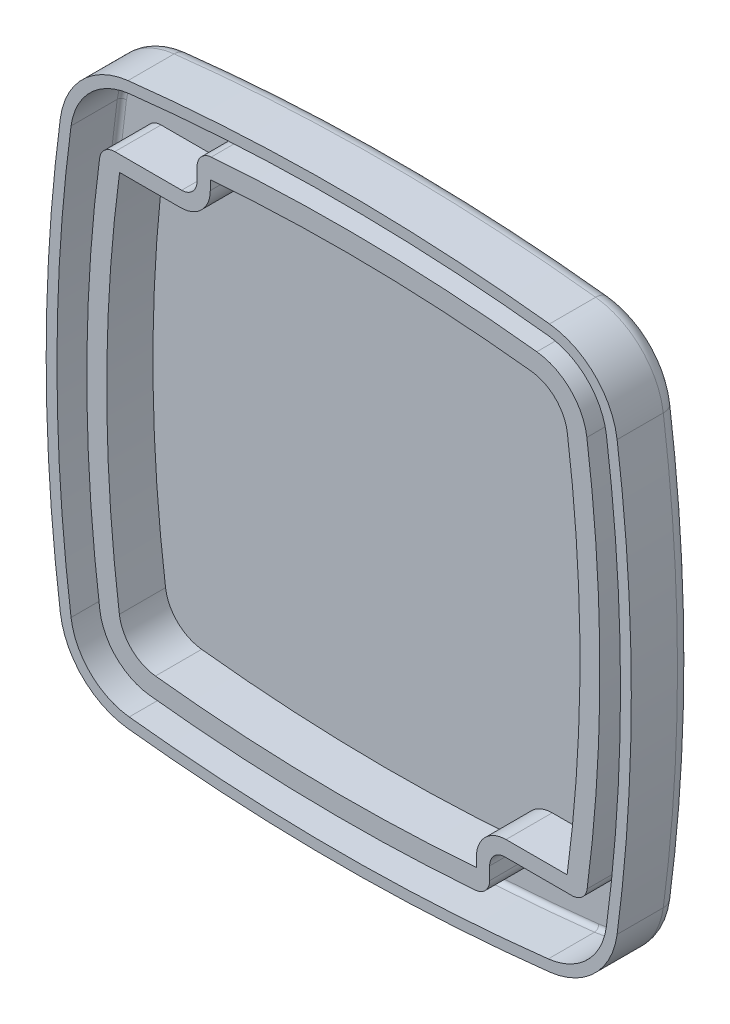
SolidWorks part; units mm, degrees
ref_plane "Ön Düzlem" through (0, 0, 0) normal (0, 0, 1) x (1, 0, 0)
ref_plane "Üst Düzlem" through (0, 0, 0) normal (0, 1, 0) x (1, 0, 0)
ref_plane "Sağ Düzlem" through (0, 0, 0) normal (1, 0, 0) x (0, 0, -1)
sketch "Çizim1" plane through (0, 0, 0) normal (0, 0, 1) x (1, 0, 0)
  line L1 (-19, -19) -> (19, -19)
  line L2 (-19, -19) -> (-19, 19)
  line L3 (-19, 19) -> (19, 19)
  line L4 (19, -19) -> (19, 19)
  line L5 (-19, -19) -> (19, 19) construction
  line L6 (-19, 19) -> (19, -19) construction
  point P0 (0, 0)
  dimension "D1" = 38
  dimension "D2" = 38
extrude "Yükseklik-Ekstrüzyon1" add sketch "Çizim1" along normal mid plane 4 contours L3 L4 L1 L2
sketch "Çizim2" plane through (0, 0, 2) normal (0, 0, 1) x (1, 0, 0)
  line L0 (-19, 17.5) -> (19, 17.5) construction
  line L1 (-19, -19) -> (-19, 19) construction
  line L2 (19, -19) -> (19, 19) construction
  line L3 (-19, 19) -> (19, 19) construction
  line L4 (0, 0) -> (12.6557, 0) construction
  line L5 (-19, 19) -> (19, 19)
  line L6 (19, 19) -> (19, 17.5)
  line L7 (-19, 19) -> (-19, 17.5)
  line L8 (-19, -17.5) -> (19, -17.5) construction
  line L9 (-19, -19) -> (-19, -17.5)
  line L10 (19, -19) -> (19, -17.5)
  line L11 (-19, -19) -> (19, -19)
  arc A0 (-19, 17.5) -> (19, 17.5) centre (0, -102.0833) cw
  arc A1 (-19, -17.5) -> (19, -17.5) centre (0, 102.0833) ccw
  line M4 (-19, 19) -> (-19, -19)
  line M5 (-19, -19) -> (19, -19)
  line M6 (19, -19) -> (19, 19)
  line M7 (19, 19) -> (-19, 19)
  dimension "D1" = 1.5
extrude "Kes-Ekstrüzyon1" cut sketch "Çizim2" against normal through all contours A0 M7 M6 | A0 L5 M4 | A1 M4 M5 | A1 L11 M6
sketch "Çizim3" plane through (0, 0, 2) normal (0, 0, 1) x (1, 0, 0)
  line L0 (17.5, 17.7287) -> (17.5, -17.7287) construction
  line L1 (19, -17.5) -> (19, 17.5) construction
  line L2 (19, 17.5) -> (19, -17.5)
  line L3 (0, 0) -> (0, -12.7146) construction
  line L4 (-17.5, 17.7287) -> (-17.5, -17.7287) construction
  line L5 (-19, 17.5) -> (-19, -17.5)
  arc A0 (19, 17.5) -> (-19, 17.5) centre (0, -102.0833) ccw construction
  arc A1 (-19, -17.5) -> (19, -17.5) centre (0, 102.0833) ccw construction
  arc A2 (17.5, 17.7287) -> (17.5, -17.7287) centre (-86.5189, 0) cw
  arc A3 (17.5, -17.7287) -> (19, -17.5) centre (0, 102.0833) ccw
  arc A4 (19, 17.5) -> (17.5, 17.7287) centre (0, -102.0833) ccw
  arc A5 (-19, 17.5) -> (-17.5, 17.7287) centre (0, -102.0833) cw
  arc A6 (-17.5, -17.7287) -> (-19, -17.5) centre (0, 102.0833) cw
  arc A7 (-17.5, 17.7287) -> (-17.5, -17.7287) centre (86.5189, 0) ccw
  arc M3 (-19, -17.5) -> (19, -17.5) centre (0, 102.0833) ccw
  line M4 (19, -17.5) -> (19, 17.5)
  arc M5 (19, 17.5) -> (-19, 17.5) centre (0, -102.0833) ccw
  line M6 (-19, 17.5) -> (-19, -17.5)
  dimension "D1" = 1.5
extrude "Kes-Ekstrüzyon2" cut sketch "Çizim3" against normal through all contours A2 L2 M5 | A2 M4 M3 | A7 L5 M3 | A7 M5 M6
fillet "Radyus1" radius 5 4 edges at (-17.5, -17.7287, 0) (17.5, -17.7287, 0) (-17.5, 17.7287, 0) (17.5, 17.7287, 0)
fillet "Radyus2" radius 1 8 edges at (16.6239, 16.8249, -2) (0, 19, -2) (-16.6239, 16.8249, -2) (-19, 0, -2) (-16.6239, -16.8249, -2) (0, -19, -2) (16.6239, -16.8249, -2) (19, 0, -2)
shell "İç Boşaltma1" thickness 0.7
sketch "Çizim10" plane through (0, 0, -1.3) normal (0, 0, 1) x (1, 0, 0)
  arc A21 (12.5637, 15.9476) -> (-12.5637, 15.9476) centre (0, -94.4838) ccw
  arc A22 (-12.5637, 15.9476) -> (-15.8151, 12.7573) centre (-12.1452, 12.2691) ccw
  arc A23 (-15.8151, 12.7573) -> (-15.8151, -12.7573) centre (80.0781, 0) ccw
  arc A24 (-15.8151, -12.7573) -> (-12.5637, -15.9476) centre (-12.1452, -12.2691) ccw
  arc A25 (-12.5637, -15.9476) -> (12.5637, -15.9476) centre (0, 94.4838) ccw
  arc A26 (12.5637, -15.9476) -> (15.8151, -12.7573) centre (12.1452, -12.2691) ccw
  arc A27 (15.8151, -12.7573) -> (15.8151, 12.7573) centre (-80.0781, 0) ccw
  arc A28 (15.8151, 12.7573) -> (12.5637, 15.9476) centre (12.1452, 12.2691) ccw
extrude "Yükseklik-Ekstrüzyon10" add sketch "Çizim10" along normal blind 3 separate body
sketch "Çizim14" plane through (0, 0, 1.7) normal (0, 0, 1) x (1, 0, 0)
  line L0 (9.5, -17.1665) -> (14.8187, -15.9691)
  line L3 (-16.5262, 13.5) -> (-9.5, 13.5)
  line L4 (-9.5, 17.1242) -> (-9.5, 13.5)
  line L5 (-9.5, 17.1242) -> (-15.4929, 15.319)
  line L6 (-15.4929, 15.319) -> (-16.5262, 13.5)
  line L7 (16.5744, -13.5) -> (9.5, -13.5)
  line L8 (9.5, -17.1665) -> (9.5, -13.5)
  line L9 (14.8187, -15.9691) -> (16.5744, -13.5)
  arc A0 (18.0784, -13.9153) -> (18.0784, 13.9153) centre (-86.5189, 0) ccw construction
  arc A1 (-13.6873, -18.2239) -> (13.6873, -18.2239) centre (0, 102.0833) ccw construction
  arc A2 (13.6873, 18.2239) -> (-13.6873, 18.2239) centre (0, -102.0833) ccw construction
  arc A3 (-18.0784, 13.9153) -> (-18.0784, -13.9153) centre (86.5189, 0) ccw construction
  point P11 (19, 0)
  point P15 (0, -19)
  point P18 (0, 19)
  point P23 (-19, 0)
  dimension "D1" = 13.5
  dimension "D2" = 9.5
  dimension "D3" = 9.5
  dimension "D4" = 13.5
extrude "Kes-Ekstrüzyon6" cut sketch "Çizim14" against normal up to surface (3 mm away) up to face at (0, 0, -1.3)
fillet "Radyus3" radius 1 6 edges at (-15.6368, 13.5, 0.2) (-9.5, 13.5, 0.2) (-9.5, 16.2532, 0.2) (9.5, -16.2532, 0.2) (9.5, -13.5, 0.2) (15.6368, -13.5, 0.2)
sketch "Çizim15" plane through (0, 0, 1.7) normal (0, 0, 1) x (1, 0, 0)
  line L8 (8.6436, -15.0198) -> (8.6436, -14.406)
  line L9 (10.5644, -12.4852) -> (14.5299, -12.4852)
  line L10 (-8.6436, 15.0198) -> (-8.6436, 14.406)
  line L11 (-10.5644, 12.4852) -> (-14.5299, 12.4852)
  arc A20 (-14.5299, 12.4852) -> (-14.5468, 12.3755) centre (-11.9023, 12.0237) ccw
  arc A21 (-14.5468, 12.3755) -> (-14.5468, -12.3755) centre (78.4765, 0) ccw
  arc A22 (-14.5468, -12.3755) -> (-12.2039, -14.6744) centre (-11.9023, -12.0237) ccw
  arc A23 (-12.2039, -14.6744) -> (8.6436, -15.0198) centre (0, 92.5941) ccw
  arc A24 (10.5644, -12.4852) -> (8.6436, -14.406) centre (10.5644, -14.406) ccw
  arc A25 (14.5299, -12.4852) -> (14.5468, -12.3755) centre (11.9023, -12.0237) ccw
  arc A26 (14.5468, -12.3755) -> (14.5468, 12.3755) centre (-78.4765, 0) ccw
  arc A27 (14.5468, 12.3755) -> (12.2039, 14.6744) centre (11.9023, 12.0237) ccw
  arc A28 (12.2039, 14.6744) -> (-8.6436, 15.0198) centre (0, -92.5941) ccw
  arc A29 (-10.5644, 12.4852) -> (-8.6436, 14.406) centre (-10.5644, 14.406) ccw
extrude "Kes-Ekstrüzyon7" cut sketch "Çizim15" against normal blind 3
